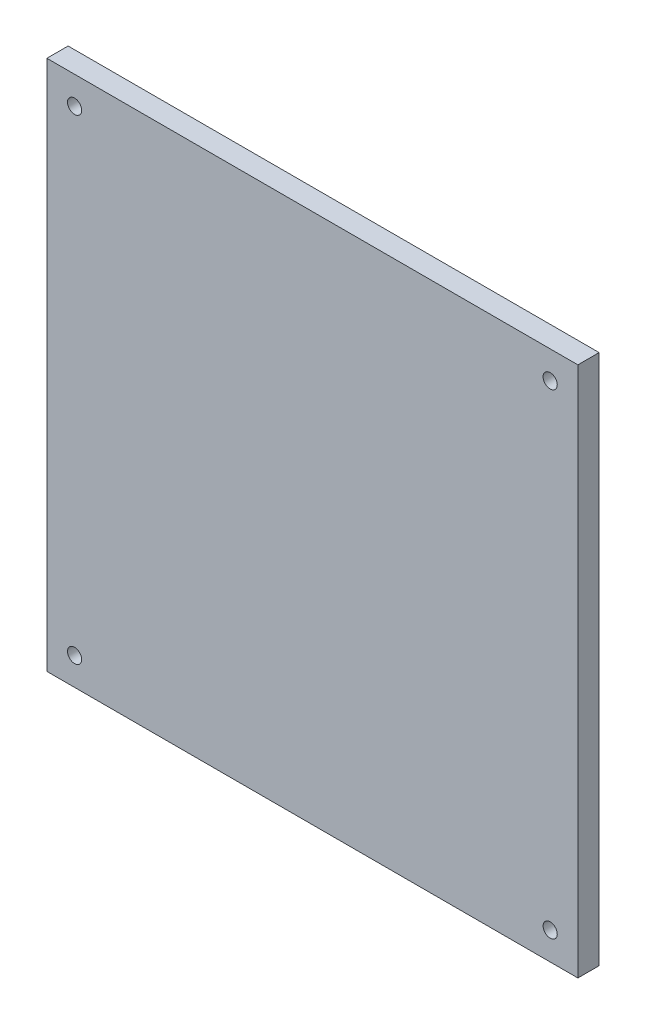
SolidWorks part; units mm, degrees
ref_plane "Front Plane" through (0, 0, 0) normal (0, 0, 1) x (1, 0, 0)
ref_plane "Top Plane" through (0, 0, 0) normal (0, 1, 0) x (1, 0, 0)
ref_plane "Right Plane" through (0, 0, 0) normal (1, 0, 0) x (0, 0, -1)
sketch "Sketch1" plane through (0, 0, 0) normal (0, 0, 1) x (1, 0, 0)
  line L1 (-75, -75) -> (75, -75)
  line L2 (-75, -75) -> (-75, 75)
  line L3 (-75, 75) -> (75, 75)
  line L4 (75, -75) -> (75, 75)
  line L5 (-75, -75) -> (75, 75) construction
  line L6 (-75, 75) -> (75, -75) construction
  point P0 (0, 0)
  dimension "D1" = 150
  dimension "D2" = 150
extrude "Boss-Extrude1" add sketch "Sketch1" along normal blind 6
sketch "Sketch2" plane through (0, 0, 6) normal (0, 0, 1) x (1, 0, 0)
  line L0 (75, 75) -> (-75, -75) construction
  line L1 (-75, 75) -> (75, -75) construction
  circle A0 centre (67.1751, 67.1751) radius 2
  circle A1 centre (67.1751, -67.1751) radius 2
  circle A2 centre (-67.1751, -67.1751) radius 2
  circle A3 centre (-67.1751, 67.1751) radius 2
  point P20 (0, 0)
  dimension "D1" = 4
  dimension "D2" = 95
  dimension "D3" = 4
extrude "Cut-Extrude1" cut sketch "Sketch2" against normal blind 10
